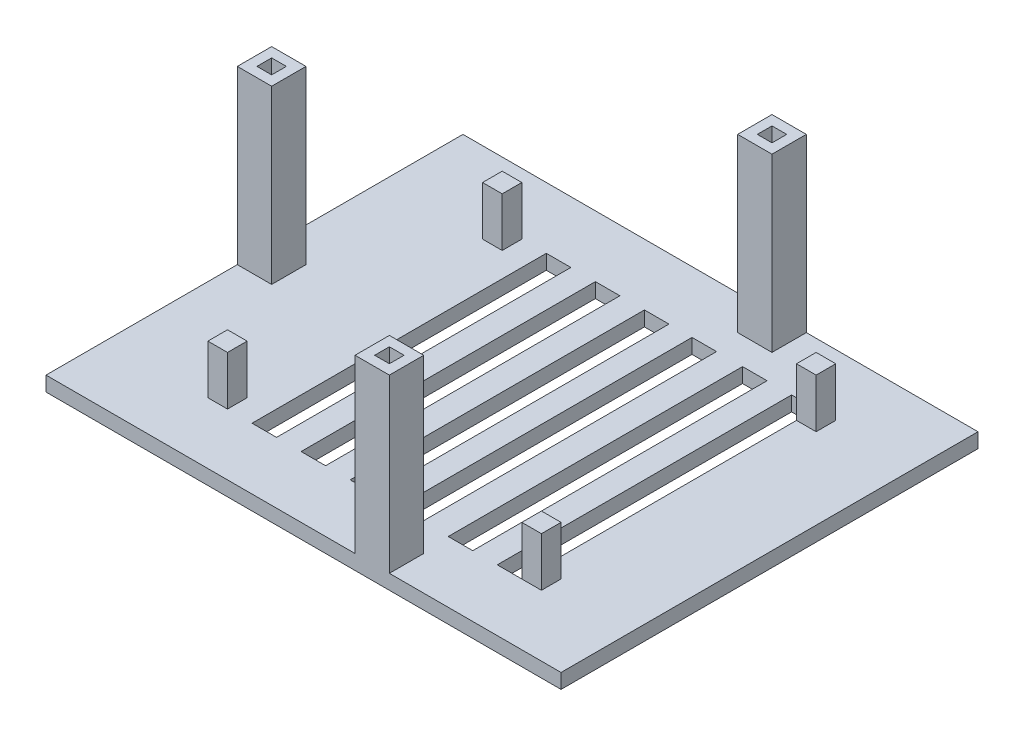
SolidWorks part; units mm, degrees
ref_plane "Front Plane" through (0, 0, 0) normal (0, 0, 1) x (1, 0, 0)
ref_plane "Top Plane" through (0, 0, 0) normal (0, 1, 0) x (1, 0, 0)
ref_plane "Right Plane" through (0, 0, 0) normal (1, 0, 0) x (0, 0, -1)
sketch "Sketch2" plane through (0, 0, 0) normal (0, 1, 0) x (1, 0, 0)
  line L0 (-54.8169, 19.6012) -> (50.1831, 19.6012)
  line L1 (50.1831, 19.6012) -> (50.1831, -65.3988)
  line L2 (-54.8169, 19.6012) -> (-54.8169, -65.3988)
  line L3 (-54.8169, -65.3988) -> (50.1831, -65.3988)
sketch "Sketch3" plane through (0, 0, 0) normal (0, 1, 0) x (1, 0, 0)
  line L0 (-54.8169, 19.6012) -> (50.1831, 19.6012)
  line L1 (50.1831, 19.6012) -> (50.1831, -65.3988)
  line L2 (50.1831, -65.3988) -> (-54.8169, -65.3988)
  line L3 (-54.8169, -65.3988) -> (-54.8169, 19.6012)
extrude "Boss-Extrude3" add sketch "Sketch3" along normal blind 3 contours L3 L0 L1 L2
ref_plane "Plane3" through (-54.8169, 3, 65.3988) normal (-1, 0, 0) x (0, 0, 1)
sketch "Sketch5" plane through (0, 3, 0) normal (0, 1, 0) x (1, 0, 0)
  line L0 (50.1831, -65.3988) -> (15.1831, -65.3988)
  line L2 (50.1831, -65.3988) -> (-54.8169, -65.3988) construction
  line L3 (15.1831, -65.3988) -> (15.1831, -58.3988)
  line L4 (15.1831, -58.3988) -> (8.1831, -58.3988)
  line L5 (8.1831, -58.3988) -> (8.1831, -65.3988)
  line L6 (10.1831, -60.3988) -> (10.1831, -63.3988)
  line L14 (13.1831, -60.3988) -> (13.1831, -63.3988)
  line L15 (13.1831, -60.3988) -> (10.1831, -60.3988)
  line L16 (10.1831, -63.3988) -> (13.1831, -63.3988)
  line L17 (8.1831, -65.3988) -> (15.1831, -65.3988)
  line M10 (-54.8169, -65.3988) -> (50.1831, -65.3988)
extrude "Boss-Extrude4" add sketch "Sketch5" along normal blind 35 contours L4 L5 L3 L16 L6 L15 L14 M10
sketch "Sketch9" plane through (0, 3, 0) normal (0, 1, 0) x (1, 0, 0)
  line L0 (50.1831, 19.6012) -> (15.1831, 19.6012)
  line L1 (-54.8169, 19.6012) -> (50.1831, 19.6012) construction
  line L2 (15.1831, 19.6012) -> (15.1831, 12.6012)
  line L3 (15.1831, 12.6012) -> (8.1831, 12.6012)
  line L4 (8.1831, 12.6012) -> (8.1831, 19.6012)
  line L5 (8.1831, 19.6012) -> (15.1831, 19.6012)
  line L6 (15.1831, 19.6012) -> (8.1831, 19.6012)
  line L7 (8.1831, 19.6012) -> (15.1831, 19.6012)
  line L8 (8.1831, 19.6012) -> (8.1831, 17.6003)
  line L9 (13.1873, 17.6003) -> (10.1884, 17.6003)
  line L11 (13.1873, 17.6003) -> (13.1873, 14.605)
  line L12 (13.1873, 14.605) -> (10.1884, 14.605)
  line L13 (10.1884, 14.605) -> (10.1884, 17.6003)
  line M7 (50.1831, 19.6012) -> (-54.8169, 19.6012)
extrude "Boss-Extrude5" add sketch "Sketch9" along normal blind 35 contours L4 L3 L2 L12 L13 L9 L11 M7
sketch "Sketch11" plane through (0, 3, 0) normal (0, 1, 0) x (1, 0, 0)
  line L0 (-54.8169, -65.3988) -> (-54.8169, 19.6012) construction
  line L1 (-54.8169, 19.6012) -> (-54.8169, -19.3988)
  line L2 (-54.8169, -19.3988) -> (-47.8169, -19.3988)
  line L3 (-47.8169, -19.3988) -> (-47.8169, -26.3988)
  line L4 (-47.8169, -26.3988) -> (-54.8169, -26.3988)
  line L5 (-54.8169, -26.3988) -> (-54.8169, -19.3988)
  line L8 (-49.8169, -21.3988) -> (-49.8169, -24.3988)
  line L9 (-49.8169, -24.3988) -> (-52.8169, -24.3988)
  line L10 (-52.8169, -24.3988) -> (-52.8169, -21.3988)
  line L11 (-52.8169, -21.3988) -> (-49.8169, -21.3988)
  line M15 (-54.8169, 19.6012) -> (-54.8169, -65.3988)
extrude "Boss-Extrude6" add sketch "Sketch11" along normal blind 35 contours L4 L3 L2 L10 L11 L8 L9 M15
sketch "Sketch12" plane through (0, 3, 0) normal (0, 1, 0) x (1, 0, 0)
  line L0 (11.6831, 12.6012) -> (11.6831, 5.1012)
  line L1 (15.1831, -58.3988) -> (8.1831, -58.3988) construction
  line L8 (-34.3169, 5.1012) -> (-32.3169, 5.1012)
  line L9 (11.6831, -58.3988) -> (11.6831, -50.8988)
  line L10 (15.1831, 12.6012) -> (8.1831, 12.6012) construction
  line L11 (29.6831, -52.8988) -> (24.6831, -52.8988)
  line L12 (11.6831, -50.8988) -> (-34.3169, -50.8988)
  line L13 (11.6831, 5.1012) -> (-34.3169, 5.1012)
  line L16 (31.6831, -48.8988) -> (29.6831, -48.8988)
  line L17 (31.6831, -52.8988) -> (29.6831, -52.8988)
  line L18 (29.6831, -52.8988) -> (29.6831, -48.8988)
  line L19 (31.6831, -48.8988) -> (33.6831, -48.8988)
  line L20 (31.6831, -52.8988) -> (33.6831, -52.8988)
  line L21 (33.6831, -52.8988) -> (33.6831, -48.8988)
  line L22 (29.6831, 7.1012) -> (24.6831, 7.1012)
  line L23 (31.6831, 3.1012) -> (29.6831, 3.1012)
  line L24 (31.6831, 3.1012) -> (33.6831, 3.1012)
  line L25 (31.6831, 7.1012) -> (33.6831, 7.1012)
  line L26 (33.6831, 7.1012) -> (29.6831, 7.1012)
  line L27 (29.6831, 7.1012) -> (29.6831, 3.1012)
  line L28 (33.6831, 3.1012) -> (33.6831, 7.1012)
  line L29 (24.6831, -52.8988) -> (24.6831, 7.1012)
  line L30 (29.6831, -48.8988) -> (29.6831, 3.1012)
extrude "Cut-Extrude1" cut sketch "Sketch12" against normal blind 6 contours L18 L30 L27 L22 L29 L11
sketch "Sketch14" plane through (0, 3, 0) normal (0, 1, 0) x (1, 0, 0)
  line L0 (24.6831, -52.8988) -> (19.6831, -52.8988)
  line L1 (19.6831, 7.1012) -> (19.6831, -52.8988)
  line L2 (24.6831, 7.1012) -> (19.6831, 7.1012)
  line L3 (19.6831, -52.8988) -> (14.6831, -52.8988)
  line L4 (19.6831, 7.1012) -> (14.6831, 7.1012)
  line L5 (14.6831, -52.8988) -> (14.6831, 7.1012)
  line L6 (14.6831, 7.1012) -> (9.6831, 7.1012)
  line L7 (14.6831, -52.8988) -> (9.6831, -52.8988)
  line L8 (9.6831, 7.1012) -> (9.6831, -52.8988)
  line L9 (9.6831, -52.8988) -> (4.6831, -52.8988)
  line L10 (4.6831, -52.8988) -> (4.6831, 7.1012)
  line L11 (4.6831, 7.1012) -> (8.6632, 7.1012)
  line L12 (4.6831, -52.8988) -> (-0.3169, -52.8988)
  line L13 (4.6831, 7.1012) -> (-0.3169, 7.1012)
  line L14 (-0.3169, 7.1012) -> (-0.3169, -52.8988)
  line L15 (-0.3169, -52.8988) -> (-5.3169, -52.8988)
  line L16 (-5.3169, -52.8988) -> (-5.3169, 7.1012)
  line L17 (-5.3169, 7.1012) -> (-0.3169, 7.1012)
  line L18 (-5.3169, -52.8988) -> (-10.3169, -52.8988)
  line L19 (-10.3169, -52.8988) -> (-10.3169, 7.1012)
  line L20 (-10.3169, 7.1012) -> (-5.3169, 7.1012)
  line L21 (-10.3169, -52.8988) -> (-15.3169, -52.8988)
  line L22 (-10.3169, 7.1012) -> (-15.3169, 7.1012)
  line L23 (-15.3169, 7.1012) -> (-15.3169, -52.8988)
  line L24 (-15.3169, -52.8988) -> (-20.3169, -52.8988)
  line L25 (-15.3169, 7.1012) -> (-20.3169, 7.1012)
  line L26 (-20.3169, 7.1012) -> (-20.3169, -52.8988)
  line L27 (-20.3169, -52.8988) -> (-25.3169, -52.8988)
  line L28 (-25.3169, -52.8988) -> (-25.3169, 7.1012)
  line L29 (-25.3169, 7.1012) -> (-20.3169, 7.1012)
  line L30 (-25.3169, -52.8988) -> (-30.3169, -52.8988)
  line L31 (-30.3169, -52.8988) -> (-30.3169, 7.1012)
  line L32 (-30.3169, 7.1012) -> (-25.3169, 7.1012)
  dimension "D1" = 50
extrude "Cut-Extrude3" cut sketch "Sketch14" against normal blind 33 contours L5 L3 L1 L4 | L17 L16 L15 L14 | L29 L28 L27 L26 | L22 L23 L21 L19
sketch "Sketch17" plane through (0, 3, 0) normal (0, 1, 0) x (1, 0, 0)
  line L1 (9.3828, -52.8988) -> (4.3828, -52.8988)
  line L2 (9.3828, -52.8988) -> (9.3828, 7.1012)
  line L3 (9.3828, 7.1012) -> (4.3828, 7.1012)
  line L4 (4.3828, -52.8988) -> (4.3828, 7.1012)
extrude "Cut-Extrude4" cut sketch "Sketch17" against normal blind 15 contours L1 L4 L3 L2
sketch "Sketch18" plane through (0, 3, 0) normal (0, 1, 0) x (1, 0, 0)
  line L0 (29.6831, -52.8988) -> (33.6831, -52.8988)
  line L1 (33.6831, -52.8988) -> (33.6831, -48.8988)
  line L2 (33.6831, -48.8988) -> (29.6831, -48.8988)
  line L3 (29.6831, -52.8988) -> (29.6831, 7.1012) construction
  line L4 (29.6831, 7.1012) -> (33.6831, 7.1012)
  line L5 (33.6831, 7.1012) -> (33.6831, 3.1012)
  line L6 (33.6831, 3.1012) -> (29.6831, 3.1012)
  line L7 (29.6831, -52.8988) -> (29.6831, -48.8988)
  line L8 (29.6831, 3.1012) -> (29.6831, 7.1012)
  line L10 (-30.3169, 7.1012) -> (-30.3169, 3.1012)
  line L11 (-30.3169, 3.1012) -> (-34.3169, 3.1012)
  line L12 (-30.3169, 7.1012) -> (-34.3169, 7.1012)
  line L13 (-34.3169, 7.1012) -> (-34.3169, 3.1012)
  line L15 (-30.3169, -52.8988) -> (-30.3169, -48.8988)
  line L16 (-30.3169, -52.8988) -> (-34.3169, -52.8988)
  line L17 (-34.3169, -52.8988) -> (-34.3169, -48.8988)
  line L18 (-34.3169, -48.8988) -> (-30.3169, -48.8988)
extrude "Boss-Extrude7" add sketch "Sketch18" along normal blind 10
